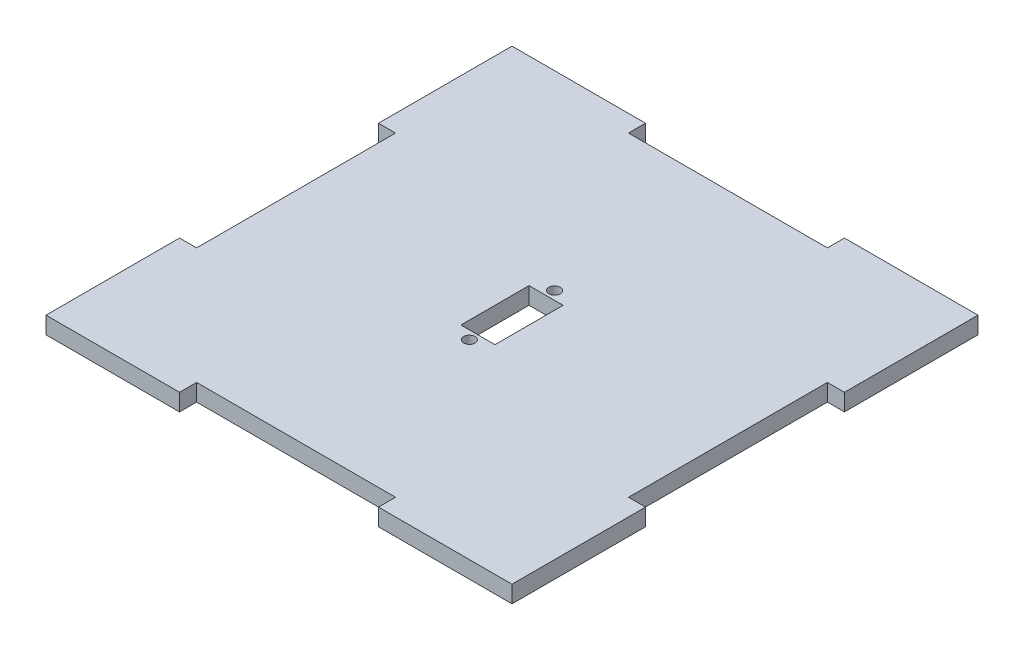
SolidWorks part; units mm, degrees
ref_plane "Front Plane" through (0, 0, 0) normal (0, 0, 1) x (1, 0, 0)
ref_plane "Top Plane" through (0, 0, 0) normal (0, 1, 0) x (1, 0, 0)
ref_plane "Right Plane" through (0, 0, 0) normal (1, 0, 0) x (0, 0, -1)
sketch "Sketch1" plane through (0, 0, 0) normal (0, 1, 0) x (1, 0, 0)
  line L0 (0, 38) -> (0, -38) construction
  line L1 (-41, -41) -> (-17.5, -41)
  line L2 (-41, -41) -> (-41, -17.5)
  line L3 (-41, 41) -> (-17.5, 41)
  line L4 (41, -41) -> (41, -17.5)
  line L5 (-41, -41) -> (41, 41) construction
  line L6 (-41, 41) -> (41, -41) construction
  line L11 (-41, 17.5) -> (-38, 17.5)
  line L12 (-38, 17.5) -> (-38, -17.5)
  line L13 (-35, 0) -> (38, 0) construction
  line L26 (17.5, 41) -> (41, 41)
  line L27 (41, 17.5) -> (41, 41)
  line L28 (17.5, -41) -> (41, -41)
  line L29 (-41, 17.5) -> (-41, 41)
  line L30 (-38, -17.5) -> (-41, -17.5)
  line L31 (-17.5, 41) -> (-17.5, 38)
  line L32 (-17.5, 38) -> (17.5, 38)
  line L33 (17.5, 38) -> (17.5, 41)
  line L34 (41, 17.5) -> (38, 17.5)
  line L35 (38, 17.5) -> (38, -17.5)
  line L36 (38, -17.5) -> (41, -17.5)
  line L37 (17.5, -41) -> (17.5, -38)
  line L38 (17.5, -38) -> (-17.5, -38)
  line L39 (-17.5, -38) -> (-17.5, -41)
  point P0 (0, 0)
  point P6 (0, 0)
  dimension "D1" = 3
  dimension "D2" = 82
  dimension "D3" = 3
  dimension "D4" = 82
  dimension "D5" = 3
  dimension "D6" = 3
extrude "Boss-Extrude1" add sketch "Sketch1" along normal blind 3
sketch "Sketch2" plane through (0, 3, 0) normal (0, 1, 0) x (1, 0, 0)
  line L0 (-38, 0) -> (38, 0) construction
  line L9 (-3, 6) -> (3, 6)
  line L10 (-3, 6) -> (-3, -6)
  line L11 (-3, -6) -> (3, -6)
  line L12 (3, 6) -> (3, -6)
  line L13 (-3, 6) -> (3, -6) construction
  line L14 (-3, -6) -> (3, 6) construction
  line L15 (-38, 17.5) -> (-38, -17.5) construction
  line L16 (38, -17.5) -> (38, 17.5) construction
  circle A6 centre (0, 7.5) radius 1
  circle A7 centre (0, -7.5) radius 1
  point P0 (0, 0)
  dimension "D3" = 7.5
  dimension "D4" = 2
  dimension "D1" = 12
  dimension "D2" = 6
extrude "Cut-Extrude1" cut sketch "Sketch2" against normal blind 3
